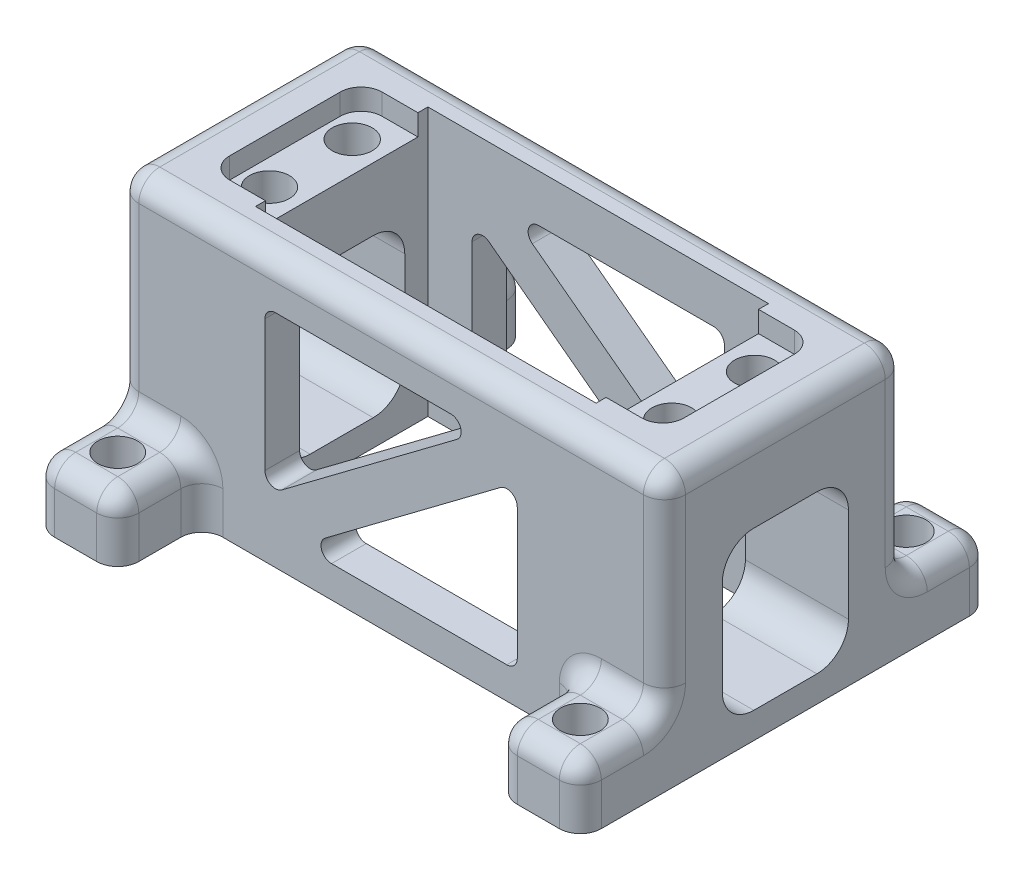
SolidWorks part; units mm, degrees
material "Olin QEA Filament - 40% infill "
ref_plane "Front Plane" through (0, 0, 0) normal (0, 0, 1) x (1, 0, 0)
ref_plane "Top Plane" through (0, 0, 0) normal (0, 1, 0) x (1, 0, 0)
ref_plane "Right Plane" through (0, 0, 0) normal (1, 0, 0) x (0, 0, -1)
sketch "Sketch1" plane through (0, 0, 0) normal (0, 1, 0) x (1, 0, 0)
  line L9 (-20.574, 10.414) -> (20.574, 10.414)
  line L10 (-20.574, 10.414) -> (-20.574, -10.414)
  line L11 (-20.574, -10.414) -> (20.574, -10.414)
  line L12 (20.574, 10.414) -> (20.574, -10.414)
  line L13 (-20.574, 10.414) -> (20.574, -10.414) construction
  line L14 (-20.574, -10.414) -> (20.574, 10.414) construction
  line L15 (-33.02, 14.605) -> (33.02, 14.605)
  line L16 (-33.02, 14.605) -> (-33.02, -14.605)
  line L17 (-33.02, -14.605) -> (33.02, -14.605)
  line L18 (33.02, 14.605) -> (33.02, -14.605)
  line L19 (-33.02, 14.605) -> (33.02, -14.605) construction
  line L20 (-33.02, -14.605) -> (33.02, 14.605) construction
  point P0 (0, 0)
  point P6 (0, 0)
  dimension "D1" = 41.148
  dimension "D2" = 20.828
  dimension "D3" = 66.04
  dimension "D4" = 29.21
extrude "Boss-Extrude1" add sketch "Sketch1" along normal blind 32.385
sketch "Sketch2" plane through (0, 32.385, 0) normal (0, 1, 0) x (1, 0, 0)
  line L0 (0, 14.605) -> (0, -14.605) construction
  line L1 (33.02, 14.605) -> (-33.02, 14.605) construction
  line L2 (-33.02, -14.605) -> (33.02, -14.605) construction
  line L3 (20.574, -10.414) -> (20.574, 10.414) construction
  line L4 (20.574, 9.2075) -> (24.892, 9.2075)
  line L5 (20.574, 9.2075) -> (20.574, -9.2075)
  line L6 (20.574, -9.2075) -> (24.892, -9.2075)
  line L7 (27.432, 6.6675) -> (27.432, -6.6675)
  line L8 (-20.574, -9.2075) -> (-24.892, -9.2075)
  line L9 (-27.432, 6.6675) -> (-27.432, -6.6675)
  line L10 (-20.574, 9.2075) -> (-24.892, 9.2075)
  line L11 (-20.574, 9.2075) -> (-20.574, -9.2075)
  arc A0 (24.892, -9.2075) -> (27.432, -6.6675) centre (24.892, -6.6675) ccw
  arc A1 (24.892, 9.2075) -> (27.432, 6.6675) centre (24.892, 6.6675) cw
  arc A2 (-24.892, -9.2075) -> (-27.432, -6.6675) centre (-24.892, -6.6675) cw
  arc A3 (-24.892, 9.2075) -> (-27.432, 6.6675) centre (-24.892, 6.6675) ccw
  point P12 (20.574, 0)
  point P13 (20.574, 0)
  point P18 (27.432, 9.2075)
  dimension "D3" = 2.54
  dimension "D1" = 18.415
  dimension "D2" = 6.858
extrude "Cut-Extrude1" cut sketch "Sketch2" against normal blind 2.54
sketch "Sketch3" plane through (0, 29.845, 0) normal (0, 1, 0) x (1, 0, 0)
  line L0 (24.3, 9.2075) -> (24.3, -9.2075) construction
  line L1 (24.892, 9.2075) -> (20.574, 9.2075) construction
  line L2 (20.574, -9.2075) -> (24.892, -9.2075) construction
  line L3 (0, 10.414) -> (0, -10.414) construction
  line L6 (24.3, 5) -> (24.3, -5)
  line L7 (20.574, 10.414) -> (-20.574, 10.414) construction
  line L8 (-20.574, -10.414) -> (20.574, -10.414) construction
  line L9 (-24.3, 9.2075) -> (-24.3, -9.2075) construction
  line L10 (-24.3, 5) -> (-24.3, -5)
  circle A0 centre (24.3, 5) radius 2.413
  circle A1 centre (24.3, -5) radius 2.413
  circle A2 centre (-24.3, -5) radius 2.413
  circle A3 centre (-24.3, 5) radius 2.413
  point P16 (24.3, 0)
  point P17 (24.3, 0)
  dimension "D2" = 4.826
  dimension "D3" = 4.826
  dimension "D1" = 10
  dimension "D4" = 48.6
extrude "Cut-Extrude2" cut sketch "Sketch3" against normal blind 10.16
sketch "Sketch4" plane through (0, 0, 0) normal (0, -1, 0) x (1, 0, 0)
  line L0 (0, 14.605) -> (0, -14.605) construction
  line L1 (-33.02, 14.605) -> (-22.86, 14.605)
  line L2 (-33.02, 14.605) -> (-33.02, 24.765)
  line L3 (-33.02, 24.765) -> (-22.86, 24.765)
  line L4 (-22.86, 14.605) -> (-22.86, 24.765)
  line L5 (-33.02, -14.605) -> (-22.86, -14.605)
  line L6 (-33.02, -14.605) -> (-33.02, -24.765)
  line L7 (-33.02, -24.765) -> (-22.86, -24.765)
  line L8 (-22.86, -14.605) -> (-22.86, -24.765)
  line L9 (-33.02, 14.605) -> (33.02, 14.605) construction
  line L10 (33.02, -14.605) -> (-33.02, -14.605) construction
  line L11 (33.02, -24.765) -> (22.86, -24.765)
  line L12 (22.86, -14.605) -> (22.86, -24.765)
  line L13 (33.02, -14.605) -> (22.86, -14.605)
  line L14 (33.02, -14.605) -> (33.02, -24.765)
  line L15 (33.02, 24.765) -> (22.86, 24.765)
  line L16 (22.86, 14.605) -> (22.86, 24.765)
  line L17 (33.02, 14.605) -> (22.86, 14.605)
  line L18 (33.02, 14.605) -> (33.02, 24.765)
  line M11 (33.02, 14.605) -> (-33.02, 14.605)
  dimension "D1" = 10.16
  dimension "D2" = 10.16
  dimension "D3" = 10.16
  dimension "D4" = 10.16
extrude "Boss-Extrude2" add sketch "Sketch4" against normal blind 7.62 contours L18 L15 L16 M11 | L2 L3 L4 L1 | L6 L7 L8 L5 | L12 L11 L14 L13
sketch "Sketch5" plane through (0, 0, 0) normal (0, -1, 0) x (1, 0, 0)
  line L0 (-33.02, 19.685) -> (33.02, 19.685) construction
  line L1 (-33.02, -24.765) -> (-33.02, 24.765) construction
  line L2 (33.02, 24.765) -> (33.02, -24.765) construction
  line L3 (-33.02, -19.685) -> (33.02, -19.685) construction
  line L4 (27.94, 24.765) -> (27.94, -24.765) construction
  line L5 (33.02, 24.765) -> (22.86, 24.765) construction
  line L6 (33.02, -24.765) -> (22.86, -24.765) construction
  line L7 (-27.94, -24.765) -> (-27.94, 24.765) construction
  line L8 (-33.02, -24.765) -> (-22.86, -24.765) construction
  line L9 (-33.02, 24.765) -> (-22.86, 24.765) construction
  line L10 (-22.86, -14.605) -> (-22.86, -24.765) construction
  line L11 (-22.86, 14.605) -> (-22.86, 24.765) construction
  circle A0 centre (27.94, 19.685) radius 2.3876
  circle A1 centre (27.94, -19.685) radius 2.3876
  circle A2 centre (-27.94, -19.685) radius 2.3876
  circle A3 centre (-27.94, 19.685) radius 2.3876
  point P30 (-22.86, -19.685)
  point P33 (-22.86, 19.685)
  dimension "D3" = 4.7752
  dimension "D4" = 4.7752
  dimension "D5" = 4.7752
  dimension "D6" = 4.7752
extrude "Cut-Extrude3" cut sketch "Sketch5" against normal through all contours A3 | A0 | A2 | A1
fillet "Fillet1" radius 2.54 36 edges at (22.86, 3.81, -14.605) (33.02, 7.62, -19.685) (-22.86, 3.81, -14.605) (-33.02, 7.62, 19.685) (33.02, 7.62, 19.685) (-33.02, 32.385, 0) (33.02, 32.385, 0) (33.02, 3.81, -24.765) (22.86, 3.81, -24.765) (22.86, 7.62, -19.685) (27.94, 7.62, -24.765) (27.94, 7.62, -14.605) (0, 32.385, -14.605) (33.02, 20.0025, -14.605) (-22.86, 3.81, -24.765) (-33.02, 3.81, -24.765) (-27.94, 7.62, -24.765) (-22.86, 7.62, -19.685) (-27.94, 7.62, -14.605) (-33.02, 7.62, -19.685) (-33.02, 20.0025, -14.605) (-22.86, 3.81, 24.765) (-33.02, 3.81, 24.765) (22.86, 3.81, 24.765) (33.02, 3.81, 24.765) (-27.94, 7.62, 24.765) (27.94, 7.62, 24.765) (22.86, 7.62, 19.685) (-22.86, 7.62, 19.685) (22.86, 3.81, 14.605) (-22.86, 3.81, 14.605) (-27.94, 7.62, 14.605) (27.94, 7.62, 14.605) (0, 32.385, 14.605) (33.02, 20.0025, 14.605) (-33.02, 20.0025, 14.605)
sketch "Sketch6" plane through (33.02, 0, 0) normal (1, 0, 0) x (0, 0, -1)
  line L1 (-3.81, 22.225) -> (3.81, 22.225)
  line L2 (-7.62, 18.415) -> (-7.62, 6.985)
  line L3 (-3.81, 3.175) -> (3.81, 3.175)
  line L4 (7.62, 18.415) -> (7.62, 6.985)
  line L5 (-7.62, 22.225) -> (7.62, 3.175) construction
  line L6 (-7.62, 3.175) -> (7.62, 22.225) construction
  line L7 (0, 0) -> (0, 29.845) construction
  line L8 (12.065, 29.845) -> (-12.065, 29.845) construction
  arc A0 (3.81, 3.175) -> (7.62, 6.985) centre (3.81, 6.985) ccw
  arc A1 (-7.62, 6.985) -> (-3.81, 3.175) centre (-3.81, 6.985) ccw
  arc A2 (3.81, 22.225) -> (7.62, 18.415) centre (3.81, 18.415) cw
  arc A3 (-3.81, 22.225) -> (-7.62, 18.415) centre (-3.81, 18.415) ccw
  point P0 (0, 12.7)
  dimension "D4" = 3.81
  dimension "D2" = 19.05
  dimension "D3" = 15.24
  dimension "D5" = 3.175
extrude "Cut-Extrude4" cut sketch "Sketch6" against normal through all contours A3 L2 A1 L3 A0 L4 A2 L1
sketch "Sketch9" plane through (0, 0, -14.605) normal (0, 0, -1) x (-1, 0, 0)
  line L0 (-20.32, 0) -> (20.32, 0) construction
  line L1 (-13.97, 26.67) -> (7.1967, 26.67)
  line L2 (-15.24, 25.4) -> (-15.24, 9.525)
  line L3 (-7.1967, 3.81) -> (13.97, 3.81)
  line L4 (15.24, 20.955) -> (15.24, 5.08)
  line L5 (-15.24, 26.67) -> (15.24, 3.81) construction
  line L6 (-15.24, 3.81) -> (15.24, 26.67) construction
  line L7 (0, 0) -> (0, 32.385) construction
  line L8 (-30.48, 32.385) -> (30.48, 32.385) construction
  line L9 (-7.9587, 6.096) -> (13.208, 21.971)
  line L10 (7.9587, 24.384) -> (-13.208, 8.509)
  line L11 (-4.919, 14.7258) -> (-1.871, 10.6618) construction
  arc A0 (13.208, 21.971) -> (15.24, 20.955) centre (13.97, 20.955) cw
  arc A1 (13.97, 3.81) -> (15.24, 5.08) centre (13.97, 5.08) ccw
  arc A2 (-7.9587, 6.096) -> (-7.1967, 3.81) centre (-7.1967, 5.08) ccw
  arc A3 (-13.208, 8.509) -> (-15.24, 9.525) centre (-13.97, 9.525) cw
  arc A4 (7.9587, 24.384) -> (7.1967, 26.67) centre (7.1967, 25.4) ccw
  arc A5 (-13.97, 26.67) -> (-15.24, 25.4) centre (-13.97, 25.4) ccw
  point P0 (0, 15.24)
  point P18 (-3.395, 12.6938)
  dimension "D5" = 1.27
  dimension "D1" = 3.81
  dimension "D2" = 30.48
  dimension "D3" = 22.86
  dimension "D4" = 5.08
extrude "Cut-Extrude5" cut sketch "Sketch9" against normal up to next contours L1 A4 L10 A3 L2 A5 | L9 A0 L4 A1 L3 A2
sketch "Sketch10" plane through (0, 0, 14.605) normal (0, 0, 1) x (1, 0, 0)
  line L0 (0, 0) -> (0, 29.845) construction
  line L1 (30.48, 29.845) -> (-30.48, 29.845) construction
  line L2 (-20.32, 0) -> (20.32, 0) construction
  line L3 (-13.97, 26.67) -> (7.1967, 26.67)
  line L4 (-15.24, 25.4) -> (-15.24, 9.525)
  line L5 (-7.1967, 3.81) -> (13.97, 3.81)
  line L6 (15.24, 20.955) -> (15.24, 5.08)
  line L7 (-15.24, 26.67) -> (15.24, 3.81) construction
  line L8 (-15.24, 3.81) -> (15.24, 26.67) construction
  line L9 (-7.9587, 6.096) -> (13.208, 21.971)
  line L10 (-13.208, 8.509) -> (7.9587, 24.384)
  line L11 (-3.3383, 9.5613) -> (-6.3863, 13.6253) construction
  arc A0 (-7.9587, 6.096) -> (-7.1967, 3.81) centre (-7.1967, 5.08) ccw
  arc A1 (13.97, 3.81) -> (15.24, 5.08) centre (13.97, 5.08) ccw
  arc A2 (13.208, 21.971) -> (15.24, 20.955) centre (13.97, 20.955) cw
  arc A3 (7.9587, 24.384) -> (7.1967, 26.67) centre (7.1967, 25.4) ccw
  arc A4 (-13.208, 8.509) -> (-15.24, 9.525) centre (-13.97, 9.525) cw
  arc A5 (-13.97, 26.67) -> (-15.24, 25.4) centre (-13.97, 25.4) ccw
  point P5 (0, 15.24)
  point P18 (-4.8623, 11.5933)
  dimension "D5" = 1.27
  dimension "D1" = 30.48
  dimension "D2" = 22.86
  dimension "D3" = 3.81
  dimension "D4" = 5.08
extrude "Cut-Extrude6" cut sketch "Sketch10" against normal up to next contours A2 L9 A0 L5 A1 L6 | L3 A3 L10 A4 L4 A5
